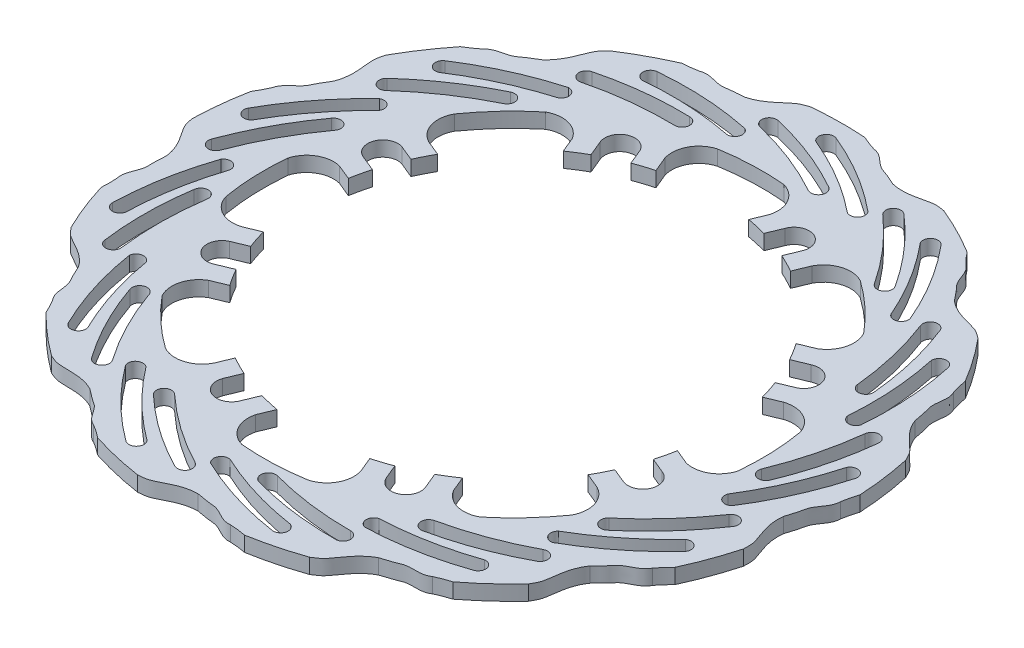
SolidWorks part; units mm, degrees
material "1.0070 (E360)"
ref_plane "Płaszczyzna XY" through (0, 0, 0) normal (0, 0, 1) x (1, 0, 0)
ref_plane "Płaszczyzna XZ" through (0, 0, 0) normal (0, 1, 0) x (1, 0, 0)
ref_plane "Płaszczyzna YZ" through (0, 0, 0) normal (1, 0, 0) x (0, 0, -1)
ref_plane "Płaszczyzna1" through (0, 5, 0) normal (0, 1, 0) x (1, 0, 0)
sketch "Szkic1" plane through (0, 5, 0) normal (0, 1, 0) x (1, 0, 0)
  line L73 (58.7717, -33.7039) -> (63.8026, -35.7878)
  line L74 (0, 0) -> (-30.7325, -18.0142) construction
  line L75 (0, 0) -> (-24.27, 101.3122) construction
  line L76 (61.7808, -27.8065) -> (66.8157, -29.892)
  line L78 (65.2035, -18.4003) -> (70.235, -20.4844)
  line L79 (55.5628, 38.7665) -> (60.5857, 40.8471)
  line L80 (59.1168, 33.0948) -> (64.1484, 35.179)
  line L81 (63.3477, 24.0234) -> (68.3827, 26.109)
  line L82 (65.3901, 17.7256) -> (70.421, 19.8095)
  line L83 (66.7009, -11.8767) -> (71.7238, -13.9573)
  line L84 (17.7256, -65.3901) -> (19.8095, -70.421)
  line L85 (24.0234, -63.3477) -> (26.109, -68.3827)
  line L86 (33.0948, -59.1168) -> (35.179, -64.1484)
  line L87 (38.7665, -55.5628) -> (40.8471, -60.5857)
  line L88 (-33.7039, -58.7717) -> (-35.7878, -63.8026)
  line L89 (-27.8065, -61.7808) -> (-29.892, -66.8157)
  line L90 (-18.4003, -65.2035) -> (-20.4844, -70.235)
  line L91 (-11.8767, -66.7009) -> (-13.9573, -71.7238)
  line L92 (-65.3901, -17.7256) -> (-70.421, -19.8095)
  line L93 (-63.3477, -24.0234) -> (-68.3827, -26.109)
  line L94 (-59.1168, -33.0948) -> (-64.1484, -35.179)
  line L95 (-55.5628, -38.7665) -> (-60.5857, -40.8471)
  line L96 (-58.7717, 33.7039) -> (-63.8026, 35.7878)
  line L97 (-61.7808, 27.8065) -> (-66.8157, 29.892)
  line L98 (-65.2035, 18.4003) -> (-70.235, 20.4844)
  line L99 (-66.7009, 11.8767) -> (-71.7238, 13.9573)
  line L100 (-17.7256, 65.3901) -> (-19.8095, 70.421)
  line L101 (-24.0234, 63.3477) -> (-26.109, 68.3827)
  line L102 (-33.0948, 59.1168) -> (-35.179, 64.1484)
  line L103 (-38.7665, 55.5628) -> (-40.8471, 60.5857)
  line L104 (33.7039, 58.7717) -> (35.7878, 63.8026)
  line L105 (27.8065, 61.7808) -> (29.892, 66.8157)
  line L106 (18.4003, 65.2035) -> (20.4844, 70.235)
  line L107 (11.8767, 66.7009) -> (13.9573, 71.7238)
  line L109 (0, 0) -> (70.421, 19.8095) construction
  line L110 (0, 0) -> (60.5857, 40.8471) construction
  arc A238 (-44.3306, 100.6718) -> (-59.9958, 92.1982) centre (0, 0) ccw
  arc A243 (68.3827, 26.109) -> (64.1484, 35.179) centre (66.2655, 30.644) ccw
  arc A246 (66.8157, -29.892) -> (70.235, -20.4844) centre (68.5254, -25.1882) ccw
  arc A249 (26.109, -68.3827) -> (35.179, -64.1484) centre (30.644, -66.2655) ccw
  arc A252 (-29.892, -66.8157) -> (-20.4844, -70.235) centre (-25.1882, -68.5254) ccw
  arc A255 (-68.3827, -26.109) -> (-64.1484, -35.179) centre (-66.2655, -30.644) ccw
  arc A258 (-66.8157, 29.892) -> (-70.235, 20.4844) centre (-68.5254, 25.1882) ccw
  arc A261 (-26.109, 68.3827) -> (-35.179, 64.1484) centre (-30.644, 66.2655) ccw
  arc A264 (29.892, 66.8157) -> (20.4844, 70.235) centre (25.1882, 68.5254) ccw
  arc A266 (82.646, -7.6575) -> (81.8577, 13.7228) centre (0, 0) ccw
  arc A267 (70.421, 19.8095) -> (81.8577, 13.7228) centre (73.2039, 11.2506) cw
  arc A268 (63.8026, -35.7878) -> (67.5856, -48.1787) centre (59.7183, -43.8076) cw
  arc A269 (19.8095, -70.421) -> (13.7228, -81.8577) centre (11.2506, -73.2039) cw
  arc A270 (-35.7878, -63.8026) -> (-48.1787, -67.5856) centre (-43.8076, -59.7183) cw
  arc A271 (-70.421, -19.8095) -> (-81.8577, -13.7228) centre (-73.2039, -11.2506) cw
  arc A272 (-63.8026, 35.7878) -> (-67.5856, 48.1787) centre (-59.7183, 43.8076) cw
  arc A273 (-19.8095, 70.421) -> (-13.7228, 81.8577) centre (-11.2506, 73.2039) cw
  arc A274 (35.7878, 63.8026) -> (48.1787, 67.5856) centre (43.8076, 59.7183) cw
  arc A275 (60.5857, 40.8471) -> (63.8542, 53.0249) centre (56.0166, 48.601) ccw
  arc A276 (71.7238, -13.9573) -> (82.646, -7.6575) centre (73.9758, -5.2436) ccw
  arc A277 (40.8471, -60.5857) -> (53.0249, -63.8542) centre (48.601, -56.0166) ccw
  arc A278 (-13.9573, -71.7238) -> (-7.6575, -82.646) centre (-5.2436, -73.9758) ccw
  arc A279 (-60.5857, -40.8471) -> (-63.8542, -53.0249) centre (-56.0166, -48.601) ccw
  arc A280 (-71.7238, 13.9573) -> (-82.646, 7.6575) centre (-73.9758, 5.2436) ccw
  arc A281 (-40.8471, 60.5857) -> (-53.0249, 63.8542) centre (-48.601, 56.0166) ccw
  arc A282 (13.9573, 71.7238) -> (7.6575, 82.646) centre (5.2436, 73.9758) ccw
  arc A283 (53.0249, -63.8542) -> (67.5856, -48.1787) centre (0, 0) ccw
  arc A284 (-7.6575, -82.646) -> (13.7228, -81.8577) centre (0, 0) ccw
  arc A285 (-63.8542, -53.0249) -> (-48.1787, -67.5856) centre (0, 0) ccw
  arc A286 (-82.646, 7.6575) -> (-81.8577, -13.7228) centre (0, 0) ccw
  arc A287 (-53.0249, 63.8542) -> (-67.5856, 48.1787) centre (0, 0) ccw
  arc A288 (7.6575, 82.646) -> (-13.7228, 81.8577) centre (0, 0) ccw
  arc A289 (63.8542, 53.0249) -> (48.1787, 67.5856) centre (0, 0) ccw
  arc A405 (-59.1168, -33.0948) -> (-55.5628, -38.7665) centre (0, 0) ccw
  arc A412 (-33.7039, -58.7717) -> (-27.8065, -61.7808) centre (0, 0) ccw
  arc A413 (-65.3901, -17.7256) -> (-63.3477, -24.0234) centre (0, 0) ccw
  arc A414 (-65.2035, 18.4003) -> (-66.7009, 11.8767) centre (0, 0) ccw
  arc A415 (-58.7717, 33.7039) -> (-61.7808, 27.8065) centre (0, 0) ccw
  arc A416 (-33.0948, 59.1168) -> (-38.7665, 55.5628) centre (0, 0) ccw
  arc A417 (-17.7256, 65.3901) -> (-24.0234, 63.3477) centre (0, 0) ccw
  arc A418 (33.7039, 58.7717) -> (27.8065, 61.7808) centre (0, 0) ccw
  arc A419 (18.4003, 65.2035) -> (11.8767, 66.7009) centre (0, 0) ccw
  arc A420 (59.1168, 33.0948) -> (55.5628, 38.7665) centre (0, 0) ccw
  arc A421 (65.3901, 17.7256) -> (63.3477, 24.0234) centre (0, 0) ccw
  arc A422 (65.2035, -18.4003) -> (66.7009, -11.8767) centre (0, 0) ccw
  arc A423 (58.7717, -33.7039) -> (61.7808, -27.8065) centre (0, 0) ccw
  arc A424 (33.0948, -59.1168) -> (38.7665, -55.5628) centre (0, 0) ccw
  arc A425 (17.7256, -65.3901) -> (24.0234, -63.3477) centre (0, 0) ccw
  arc A426 (-18.4003, -65.2035) -> (-11.8767, -66.7009) centre (0, 0) ccw
  arc A427 (-55.7088, 78.3802) -> (-56.9454, 83.2248) centre (-56.3188, 80.8046) cw
  arc A428 (-27.6037, 86.5165) -> (-27.6037, 81.5165) centre (-27.6037, 84.0165) cw
  arc A429 (-46.0826, 89.1395) -> (-46.0507, 94.115) centre (-45.8199, 91.6257) cw
  arc A430 (-46.0826, 89.1395) -> (-16.1171, 87.5772) centre (-36.4938, -15.0988) cw
  arc A431 (-15.0642, 92.3267) -> (-16.1171, 87.5772) centre (-16.1544, 90.0769) cw
  arc A432 (-46.0507, 94.115) -> (-15.0642, 92.3267) centre (-36.4689, -9.2079) cw
  arc A433 (-55.7088, 78.3802) -> (-27.6037, 81.5165) centre (-30.1417, -23.2356) cw
  arc A434 (-56.9454, 83.2248) -> (-27.6037, 86.5165) centre (-30.7325, -18.0142) cw
  arc A435 (15.7643, 89.4346) -> (13.4407, 85.0074) centre (14.6025, 87.221) cw
  arc A436 (-12.9026, 95.2914) -> (13.4407, 85.0074) centre (-37.4873, -6.5666) cw
  arc A437 (-12.9026, 95.2914) -> (-11.7462, 100.1558) centre (-12.3161, 97.7216) cw
  arc A438 (-11.7462, 100.1558) -> (15.7643, 89.4346) centre (-35.5839, -1.6687) cw
  arc A439 (0.6211, 100.3448) -> (26.4282, 85.0358) centre (-39.3305, 3.5902) cw
  arc A440 (29.5677, 88.7519) -> (26.4282, 85.0358) centre (27.5568, 87.2665) cw
  arc A441 (2.9615, 104.7355) -> (29.5677, 88.7519) centre (-36.5707, 8.7948) cw
  arc A442 (0.6211, 100.3448) -> (2.9615, 104.7355) centre (2.0091, 102.4241) cw
  arc A443 (55.521, 71.8644) -> (51.406, 69.0241) centre (53.4635, 70.4442) cw
  arc A444 (32.8594, 90.3725) -> (51.406, 69.0241) centre (-36.245, 11.6068) cw
  arc A445 (32.8594, 90.3725) -> (36.144, 94.1423) centre (34.5082, 92.2517) cw
  arc A446 (36.144, 94.1423) -> (55.521, 71.8644) centre (-32.2834, 15.0591) cw
  arc A447 (47.1825, 88.5622) -> (62.9191, 63.0136) centre (-33.1569, 21.4567) cw
  arc A448 (67.4259, 64.8452) -> (62.9191, 63.0136) centre (64.9551, 64.4644) cw
  arc A449 (51.2954, 91.3624) -> (67.4259, 64.8452) centre (-28.2946, 24.7826) cw
  arc A450 (47.1825, 88.5622) -> (51.2954, 91.3624) centre (49.3778, 89.7583) cw
  arc A451 (82.5584, 37.8309) -> (77.5949, 37.2282) centre (80.0766, 37.5295) cw
  arc A452 (71.0937, 64.7503) -> (77.5949, 37.2282) centre (-26.6994, 27.1212) cw
  arc A453 (71.0937, 64.7503) -> (75.754, 66.5619) centre (73.427, 65.6481) cw
  arc A454 (75.754, 66.5619) -> (82.5584, 37.8309) centre (-21.5872, 28.3371) cw
  arc A455 (82.935, 56.4912) -> (84.996, 26.5559) centre (-19.3876, 34.4078) cw
  arc A456 (89.8377, 26.0831) -> (84.996, 26.5559) centre (87.473, 26.8942) cw
  arc A457 (87.878, 57.0593) -> (89.8377, 26.0831) centre (-13.5366, 35.0931) cw
  arc A458 (82.935, 56.4912) -> (87.878, 57.0593) centre (85.4347, 56.53) cw
  arc A459 (90.6827, -4.8692) -> (86.0077, -3.0962) centre (88.3452, -3.9827) cw
  arc A460 (93.0413, 24.2946) -> (86.0077, -3.0962) centre (-11.0373, 36.4225) cw
  arc A461 (93.0413, 24.2946) -> (98.0097, 23.733) centre (95.5245, 24.0053) cw
  arc A462 (98.0097, 23.733) -> (90.6827, -4.8692) centre (-5.9456, 35.1233) cw
  arc A463 (99.688, 11.4786) -> (87.6013, -15.9856) centre (-1.1768, 39.4764) cw
  arc A464 (91.6688, -18.6542) -> (87.6013, -15.9856) centre (89.9518, -16.8371) cw
  arc A465 (104.3289, 9.6845) -> (91.6688, -18.6542) centre (4.3225, 37.3642) cw
  arc A466 (99.688, 11.4786) -> (104.3289, 9.6845) centre (101.9195, 10.3514) cw
  arc A467 (78.0327, -46.4539) -> (74.7171, -42.7113) centre (76.3749, -44.5826) cw
  arc A468 (93.6743, -21.7266) -> (74.7171, -42.7113) centre (7.1533, 37.3798) cw
  arc A469 (93.6743, -21.7266) -> (97.8125, -24.5328) centre (95.7386, -23.1368) cw
  arc A470 (97.8125, -24.5328) -> (78.0327, -46.4539) centre (11.058, 33.8632) cw
  arc A471 (93.6037, -36.1635) -> (70.1383, -54.8649) centre (17.3036, 35.5015) cw
  arc A472 (72.4997, -59.1181) -> (70.1383, -54.8649) centre (71.8238, -56.7112) cw
  arc A473 (96.8793, -39.9088) -> (72.4997, -59.1181) centre (21.1914, 31.0756) cw
  arc A474 (93.6037, -36.1635) -> (96.8793, -39.9088) centre (95.0557, -38.1986) cw
  arc A475 (47.5064, -77.3965) -> (46.3098, -72.5418) centre (46.9081, -74.9691) cw
  arc A476 (72.8476, -62.7706) -> (46.3098, -72.5418) centre (23.7052, 29.7738) cw
  arc A477 (72.8476, -62.7706) -> (75.2077, -67.1785) centre (74.0201, -64.9786) cw
  arc A478 (75.2077, -67.1785) -> (47.5064, -77.3965) centre (25.5284, 24.8455) cw
  arc A479 (66.076, -75.521) -> (36.6074, -81.1753) centre (31.82, 23.3936) cw
  arc A480 (36.7217, -86.0388) -> (36.6074, -81.1753) centre (37.2418, -83.5935) cw
  arc A481 (67.2358, -80.3595) -> (36.7217, -86.0388) centre (33.2056, 17.6679) cw
  arc A482 (66.076, -75.521) -> (67.2358, -80.3595) centre (66.4159, -77.9978) cw
  arc A483 (6.0969, -90.6085) -> (7.2935, -85.7538) centre (6.6952, -88.1811) cw
  arc A484 (35.3324, -89.4346) -> (7.2935, -85.7538) centre (34.8265, 15.3471) cw
  arc A485 (35.3324, -89.4346) -> (35.3737, -94.4344) centre (35.3445, -91.9345) cw
  arc A486 (35.3737, -94.4344) -> (6.0969, -90.6085) centre (34.1505, 10.1359) cw
  arc A487 (23.411, -97.5776) -> (-5.3098, -88.8895) centre (39.0468, 5.9265) cw
  arc A488 (-7.4687, -93.249) -> (-5.3098, -88.8895) centre (-5.8718, -91.3255) cw
  arc A489 (22.1894, -102.4009) -> (-7.4687, -93.249) centre (37.6128, 0.2127) cw
  arc A490 (23.411, -97.5776) -> (22.1894, -102.4009) centre (22.561, -99.9286) cw
  arc A491 (-36.7093, -83.0632) -> (-33.3937, -79.3206) centre (-35.0515, -81.1919) cw
  arc A492 (-10.277, -95.6102) -> (-33.3937, -79.3206) centre (37.9695, -2.5955) cw
  arc A493 (-10.277, -95.6102) -> (-12.564, -100.0565) centre (-11.4281, -97.8294) cw
  arc A494 (-12.564, -100.0565) -> (-36.7093, -83.0632) centre (34.9492, -6.8956) cw
  arc A495 (-24.6172, -97.2803) -> (-46.0106, -76.2401) centre (37.3284, -12.8982) cw
  arc A496 (-49.9482, -79.097) -> (-46.0106, -76.2401) centre (-47.6403, -78.1359) cw
  arc A497 (-27.9403, -100.9834) -> (-49.9482, -79.097) centre (33.4033, -17.2912) cw
  arc A498 (-24.6172, -97.2803) -> (-27.9403, -100.9834) centre (-26.4624, -98.967) cw
  arc A499 (-71.1059, -56.4891) -> (-66.4308, -54.7161) centre (-68.7684, -55.6026) cw
  arc A500 (-53.5321, -79.8826) -> (-66.4308, -54.7161) centre (32.4141, -19.9435) cw
  arc A501 (-53.5321, -79.8826) -> (-57.6234, -82.7568) centre (-55.5827, -81.3127) cw
  arc A502 (-57.6234, -82.7568) -> (-71.1059, -56.4891) centre (27.7414, -22.3475) cw
  arc A503 (-67.0058, -74.6973) -> (-76.1709, -46.1251) centre (27.0585, -28.7682) cw
  arc A504 (-80.9851, -46.8248) -> (-76.1709, -46.1251) centre (-78.495, -47.0464) cw
  arc A505 (-71.6693, -76.4318) -> (-80.9851, -46.8248) centre (21.5416, -30.8339) cw
  arc A506 (-67.0058, -74.6973) -> (-71.6693, -76.4318) centre (-69.4236, -75.3332) cw
  arc A507 (-89.2129, -16.9741) -> (-84.2494, -17.5768) centre (-86.7312, -17.2754) cw
  arc A508 (-84.5236, -45.8549) -> (-84.2494, -17.5768) centre (19.433, -32.7227) cw
  arc A509 (-84.5236, -45.8549) -> (-89.482, -46.4986) centre (-87.0039, -46.1683) cw
  arc A510 (-89.482, -46.4986) -> (-89.2129, -16.9741) centre (14.1784, -32.6798) cw
  arc A511 (-94.0443, -35.002) -> (-88.8814, -5.4433) centre (10.5899, -38.0477) cw
  arc A512 (-93.4693, -3.8256) -> (-88.8814, -5.4433) centre (-91.3674, -5.1791) cw
  arc A513 (-98.9796, -34.3706) -> (-93.4693, -3.8256) centre (4.7449, -37.3129) cw
  arc A514 (-94.0443, -35.002) -> (-98.9796, -34.3706) centre (-96.4806, -34.4415) cw
  arc A515 (-86.8824, 26.4295) -> (-82.7675, 23.5892) centre (-84.8249, 25.0094) cw
  arc A516 (-96.1518, -1.3224) -> (-82.7675, 23.5892) centre (2.0001, -38.0055) cw
  arc A517 (-96.1518, -1.3224) -> (-100.8414, 0.4119) centre (-98.4936, -0.4472) cw
  arc A518 (-100.8414, 0.4119) -> (-86.8824, 26.4295) centre (-2.6327, -35.5256) cw
  arc A519 (-99.5383, 12.7118) -> (-81.2302, 36.4854) centre (-8.3048, -38.6109) cw
  arc A520 (-84.5408, 40.0499) -> (-81.2302, 36.4854) centre (-83.3086, 37.8747) cw
  arc A521 (-103.6149, 15.5644) -> (-84.5408, 40.0499) centre (-13.1388, -35.244) cw
  arc A522 (-99.5383, 12.7118) -> (-103.6149, 15.5644) centre (-101.4351, 14.3403) cw
  arc A523 (-64.6481, 63.7784) -> (-62.3245, 59.3512) centre (-63.4863, 61.5648) cw
  arc A524 (-85.7528, 43.513) -> (-62.3245, 59.3512) centre (-15.891, -34.5817) cw
  arc A525 (-85.7528, 43.513) -> (-89.0992, 47.228) centre (-87.4196, 45.3763) cw
  arc A526 (-89.0992, 47.228) -> (-64.6481, 63.7784) centre (-18.8407, -30.2329) cw
  arc A527 (-82.2293, 57.5135) -> (-54.9702, 70.0558) centre (-25.2969, -30.3289) cw
  arc A528 (-56.2451, 74.7505) -> (-54.9702, 70.0558) centre (-56.1649, 72.2518) cw
  arc A529 (-84.5133, 61.9339) -> (-56.2451, 74.7505) centre (-28.0125, -25.1011) cw
  arc A530 (-82.2293, 57.5135) -> (-84.5133, 61.9339) centre (-83.1521, 59.837) cw
  arc A531 (67.1347, -87.1374) -> (80.3169, -75.1611) centre (0, 0) ccw
  arc A532 (18.9501, -108.3554) -> (36.188, -103.877) centre (0, 0) ccw
  arc A533 (-33.5758, -104.7505) -> (-16.2312, -108.7959) centre (0, 0) ccw
  arc A534 (-78.4099, -77.1485) -> (-64.932, -88.791) centre (0, 0) ccw
  arc A535 (-105.2812, -31.8727) -> (-98.7576, -48.4451) centre (0, 0) ccw
  arc A536 (-108.0339, 20.7047) -> (-109.9591, 2.999) centre (0, 0) ccw
  arc A537 (-86.0373, 68.539) -> (-95.9703, 53.756) centre (0, 0) ccw
  arc A538 (7.5317, 109.7418) -> (-10.277, 109.5189) centre (0, 0) ccw
  arc A539 (57.6686, 93.6714) -> (41.7961, 101.7501) centre (0, 0) ccw
  arc A540 (94.5943, 56.142) -> (84.2942, 70.6716) centre (0, 0) ccw
  arc A541 (109.8496, 5.7511) -> (107.4816, 23.4031) centre (0, 0) ccw
  arc A542 (99.9396, -45.9573) -> (106.0462, -29.2267) centre (0, 0) ccw
  spline S0 degree 3 poles (-39.0568, 101.3122) (-37.6119, 101.8457) (-34.9962, 101.55) (-31.4457, 100.3666) (-27.8863, 101.2105) (-25.6359, 101.111) (-24.27, 101.3122) knots 0 0 0 0 0.147284 0.282721 0.381948 0.523862 0.523862 0.523862 0.523862
  spline S1 degree 2 poles (-39.0568, 101.3122) (-41.5725, 100.7987) (-44.3306, 100.6718) knots 0 0 0 0.254897 0.254897 0.254897
  spline S2 degree 3 poles (-24.27, 101.3122) (-20.3733, 102.2654) (-17.209, 105.193) (-12.953, 108.7166) (-11.1408, 109.1582) (-10.277, 109.5189) knots 0 0 0 0 0.594179 0.740322 0.894848 0.894848 0.894848 0.894848
  spline S3 degree 3 poles (25.5921, 100.9863) (29.4854, 100.0194) (33.6478, 101.1412) (39.0538, 102.2833) (40.8636, 101.8322) (41.7961, 101.7501) knots 0 0 0 0 0.594179 0.740322 0.894848 0.894848 0.894848 0.894848
  spline S4 degree 3 poles (12.4991, 107.8581) (14.0264, 107.659) (16.205, 106.1816) (18.7989, 103.4837) (22.3428, 102.5768) (24.2892, 101.4429) (25.5921, 100.9863) knots 0 0 0 0 0.147284 0.282721 0.381948 0.523862 0.523862 0.523862 0.523862
  spline S5 degree 2 poles (12.4991, 107.8581) (10.0329, 108.5725) (7.5317, 109.7418) knots 0 0 0 0.254897 0.254897 0.254897
  spline S6 degree 3 poles (69.5913, 77.5257) (72.5894, 74.8603) (76.7963, 73.9192) (82.1138, 72.4182) (83.5068, 71.1777) (84.2942, 70.6716) knots 0 0 0 0 0.594179 0.740322 0.894848 0.894848 0.894848 0.894848
  spline S7 degree 3 poles (61.1915, 89.695) (62.4514, 88.8089) (63.6938, 86.4883) (64.7369, 82.894) (67.4534, 80.4441) (68.6499, 78.5355) (69.5913, 77.5257) knots 0 0 0 0 0.147284 0.282721 0.381948 0.523862 0.523862 0.523862 0.523862
  spline S8 degree 2 poles (61.1915, 89.695) (59.3398, 91.4736) (57.6686, 93.6714) knots 0 0 0 0.254897 0.254897 0.254897
  spline S9 degree 3 poles (97.6481, 36.3049) (99.064, 32.5515) (102.3517, 29.7632) (106.3626, 25.9629) (107.0195, 24.2172) (107.4816, 23.4031) knots 0 0 0 0 0.594179 0.740322 0.894848 0.894848 0.894848 0.894848
  spline S10 degree 3 poles (95.8657, 50.9838) (96.5695, 49.6138) (96.5912, 46.9816) (95.8444, 43.3143) (97.1112, 39.8825) (97.2837, 37.6366) (97.6481, 36.3049) knots 0 0 0 0 0.147284 0.282721 0.381948 0.523862 0.523862 0.523862 0.523862
  spline S11 degree 2 poles (95.8657, 50.9838) (95.0527, 53.4193) (94.5943, 56.142) knots 0 0 0 0.254897 0.254897 0.254897
  spline S12 degree 3 poles (103.3348, -13.2329) (102.8442, -17.2144) (104.4595, -21.2112) (106.245, -26.4401) (106.0153, -28.2912) (106.0462, -29.2267) knots 0 0 0 0 0.594179 0.740322 0.894848 0.894848 0.894848 0.894848
  spline S13 degree 3 poles (108.5782, 0.5929) (108.5647, -0.9473) (107.3607, -3.2881) (104.9952, -6.1882) (104.522, -9.8156) (103.631, -11.8845) (103.3348, -13.2329) knots 0 0 0 0 0.147284 0.282721 0.381948 0.523862 0.523862 0.523862 0.523862
  spline S14 degree 2 poles (108.5782, 0.5929) (108.9902, 3.1272) (109.8496, 5.7511) knots 0 0 0 0.254897 0.254897 0.254897
  spline S15 degree 3 poles (85.3488, -59.7393) (83.0641, -63.0367) (82.637, -67.3264) (81.7879, -72.7861) (80.7243, -74.3184) (80.3169, -75.1611) knots 0 0 0 0 0.594179 0.740322 0.894848 0.894848 0.894848 0.894848
  spline S16 degree 3 poles (96.4168, -49.9338) (95.6891, -51.2913) (93.5351, -52.8044) (90.0928, -54.2731) (87.9881, -57.2651) (86.2377, -58.6829) (85.3488, -59.7393) knots 0 0 0 0 0.147284 0.282721 0.381948 0.523862 0.523862 0.523862 0.523862
  spline S17 degree 2 poles (96.4168, -49.9338) (97.9593, -47.8813) (99.9396, -45.9573) knots 0 0 0 0.254897 0.254897 0.254897
  spline S18 degree 3 poles (47.8104, -92.56) (44.255, -94.4181) (41.8833, -98.0179) (38.5942, -102.4576) (36.9404, -103.3201) (36.188, -103.877) knots 0 0 0 0 0.594179 0.740322 0.894848 0.894848 0.894848 0.894848
  spline S19 degree 3 poles (62.1674, -89.0213) (60.8922, -89.8851) (58.2818, -90.224) (54.5512, -89.9247) (51.2972, -91.5958) (49.0884, -92.0378) (47.8104, -92.56) knots 0 0 0 0 0.147284 0.282721 0.381948 0.523862 0.523862 0.523862 0.523862
  spline S20 degree 2 poles (62.1674, -89.0213) (64.4871, -87.9207) (67.1347, -87.1374) knots 0 0 0 0.254897 0.254897 0.254897
  spline S21 degree 3 poles (-0.6808, -104.1764) (-4.6924, -104.1694) (-8.4654, -106.2546) (-13.4409, -108.6573) (-15.3062, -108.6525) (-16.2312, -108.7959) knots 0 0 0 0 0.594179 0.740322 0.894848 0.894848 0.894848 0.894848
  spline S22 degree 3 poles (13.6763, -107.7151) (12.1457, -107.8873) (9.6768, -106.9742) (6.5127, -104.9756) (2.8547, -104.9431) (0.6935, -104.3079) (-0.6808, -104.1764) knots 0 0 0 0 0.147284 0.282721 0.381948 0.523862 0.523862 0.523862 0.523862
  spline S23 degree 2 poles (13.6763, -107.7151) (16.2417, -107.8186) (18.9501, -108.3554) knots 0 0 0 0.254897 0.254897 0.254897
  spline S24 degree 3 poles (-49.016, -91.9272) (-52.5648, -90.0567) (-56.8747, -90.1498) (-62.3969, -89.965) (-64.0463, -89.0939) (-64.932, -88.791) knots 0 0 0 0 0.594179 0.740322 0.894848 0.894848 0.894848 0.894848
  spline S25 degree 3 poles (-37.948, -101.7327) (-39.3833, -101.1739) (-41.145, -99.218) (-43.0179, -95.9778) (-46.2418, -94.2491) (-47.8602, -92.6824) (-49.016, -91.9272) knots 0 0 0 0 0.147284 0.282721 0.381948 0.523862 0.523862 0.523862 0.523862
  spline S26 degree 2 poles (-37.948, -101.7327) (-35.7245, -103.0165) (-33.5758, -104.7505) knots 0 0 0 0.254897 0.254897 0.254897
  spline S27 degree 3 poles (-86.1223, -58.6186) (-88.3953, -55.3132) (-92.2547, -53.3927) (-97.0586, -50.6627) (-98.1141, -49.1249) (-98.7576, -48.4451) knots 0 0 0 0 0.594179 0.740322 0.894848 0.894848 0.894848 0.894848
  spline S28 degree 3 poles (-80.8788, -72.4445) (-81.89, -71.2827) (-82.541, -68.7322) (-82.6936, -64.9927) (-84.7448, -61.9638) (-85.4498, -59.8244) (-86.1223, -58.6186) knots 0 0 0 0 0.147284 0.282721 0.381948 0.523862 0.523862 0.523862 0.523862
  spline S29 degree 2 poles (-80.8788, -72.4445) (-79.5066, -74.6146) (-78.4099, -77.1485) knots 0 0 0 0.254897 0.254897 0.254897
  spline S30 degree 3 poles (-103.4989, -11.8812) (-103.9755, -7.8981) (-106.5003, -4.4039) (-109.4852, 0.2457) (-109.7052, 2.098) (-109.9591, 2.999) knots 0 0 0 0 0.594179 0.740322 0.894848 0.894848 0.894848 0.894848
  spline S31 degree 3 poles (-105.2813, -26.5602) (-105.6367, -25.0615) (-105.0279, -22.5006) (-103.4252, -19.1186) (-103.8338, -15.4834) (-103.4638, -13.2614) (-103.4989, -11.8812) knots 0 0 0 0 0.147284 0.282721 0.381948 0.523862 0.523862 0.523862 0.523862
  spline S32 degree 2 poles (-105.2813, -26.5602) (-105.0748, -29.1194) (-105.2812, -31.8727) knots 0 0 0 0.254897 0.254897 0.254897
  spline S33 degree 3 poles (-97.1652, 37.578) (-95.7361, 41.3264) (-96.348, 45.5937) (-96.8302, 51.0979) (-96.1642, 52.8402) (-95.9703, 53.756) knots 0 0 0 0 0.594179 0.740322 0.894848 0.894848 0.894848 0.894848
  spline S34 degree 3 poles (-105.5651, 25.4088) (-105.1833, 26.901) (-103.4541, 28.8856) (-100.4633, 31.1354) (-99.1358, 34.5441) (-97.7756, 36.3397) (-97.1652, 37.578) knots 0 0 0 0 0.147284 0.282721 0.381948 0.523862 0.523862 0.523862 0.523862
  spline S35 degree 2 poles (-105.5651, 25.4088) (-106.5715, 23.0467) (-108.0339, 20.7047) knots 0 0 0 0.254897 0.254897 0.254897
  spline S36 degree 3 poles (-68.5721, 78.4286) (-65.5648, 81.0835) (-64.1234, 85.1463) (-61.9925, 90.2442) (-60.5931, 91.4774) (-59.9958, 92.1982) knots 0 0 0 0 0.594179 0.740322 0.894848 0.894848 0.894848 0.894848
  spline S37 degree 3 poles (-81.6652, 71.5569) (-80.6337, 72.7008) (-78.1802, 73.6545) (-74.4865, 74.2567) (-71.7269, 76.658) (-69.6881, 77.6157) (-68.5721, 78.4286) knots 0 0 0 0 0.147284 0.282721 0.381948 0.523862 0.523862 0.523862 0.523862
  spline S38 degree 2 poles (-81.6652, 71.5569) (-83.6541, 69.9331) (-86.0373, 68.539) knots 0 0 0 0.254897 0.254897 0.254897
  dimension "D3" = 220
  dimension "D6" = 6.6
  dimension "D7" = 5.4367
  dimension "D13" = 9
  dimension "D10" = 35.623
  dimension "D5" = 6.6
  dimension "D12" = 166
  dimension "D11" = 8
  dimension "D16" = 9
  dimension "D22" = 135.5
  dimension "D4" = 10
  dimension "D8" = 5.4454
  dimension "D9" = 13
  dimension "D14" = 8
  dimension "D15" = 104.1786
  dimension "D17" = 10
  dimension "D18" = 10
  dimension "D19" = 8
extrude "Dodanie-wyciągnięcie1" add sketch "Szkic1" against normal blind 5
